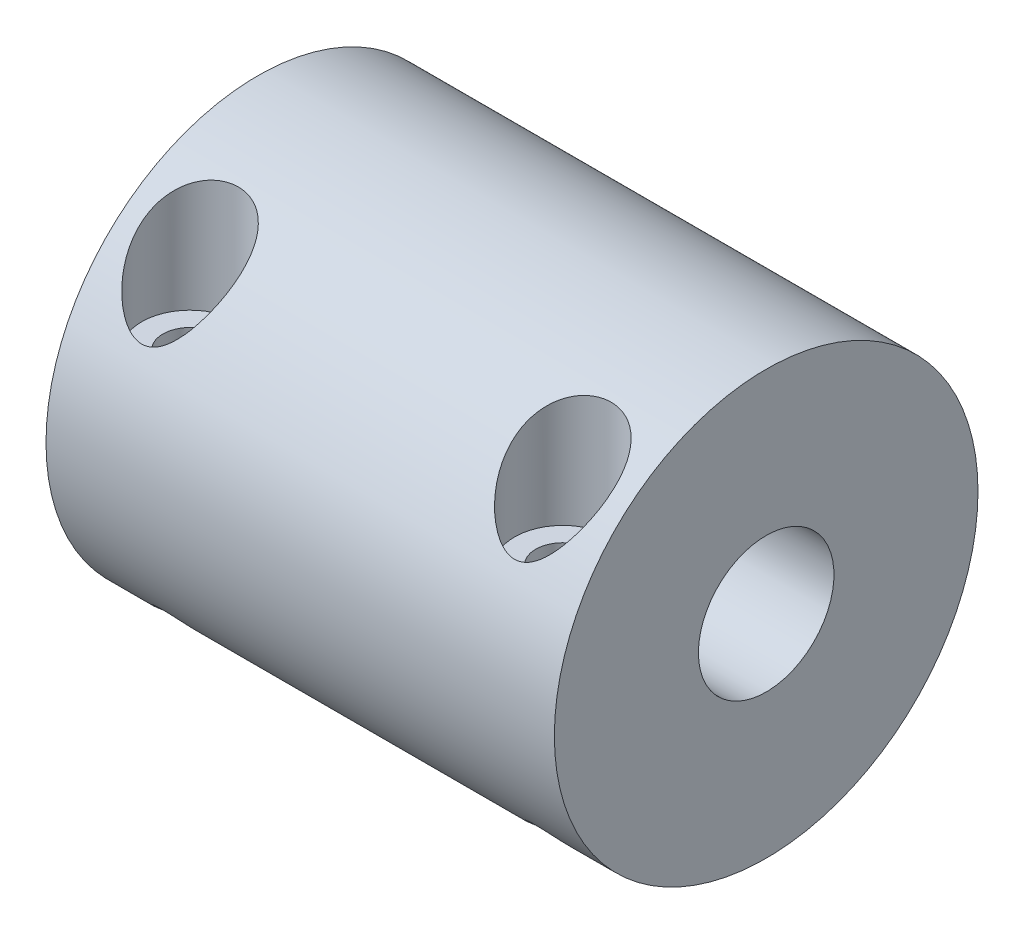
SolidWorks part; units mm, degrees
ref_plane "前视基准面" through (0, 0, 0) normal (0, 0, 1) x (1, 0, 0)
ref_plane "上视基准面" through (0, 0, 0) normal (0, 1, 0) x (1, 0, 0)
ref_plane "右视基准面" through (0, 0, 0) normal (1, 0, 0) x (0, 0, -1)
sketch "草图1" plane through (0, 0, 0) normal (0, 1, 0) x (1, 0, 0)
  line L0 (-118.9427, 0) -> (5828.1908, 0) construction
  line L1 (0, -118.9427) -> (0, 5828.1908) construction
  line L3 (0, 0) -> (30, 0)
  line L4 (0, 0) -> (0, 12.5)
  line L5 (0, 12.5) -> (30, 12.5)
  line L6 (30, 0) -> (30, 12.5)
  line L7 (0, 0) -> (30, 0)
  line L8 (0, 0) -> (0, 3)
  line L9 (0, 3) -> (30, 3)
  line L10 (30, 0) -> (30, 3)
  line L11 (30, 0) -> (15, 0)
  line L12 (30, 0) -> (30, 4)
  line L13 (30, 4) -> (15, 4)
  line L14 (15, 0) -> (15, 4)
  dimension "D1" = 8
  dimension "D2" = 6
  dimension "D3" = 25
  dimension "D4" = 30
  dimension "D5" = 30
  dimension "D6" = 15
revolve "主体" add sketch "草图1" angle 360 about L0
sketch "草图2" plane through (0, 0, 0) normal (0, 1, 0) x (1, 0, 0)
  line L0 (-1000, 0) -> (49000, 0) construction
  line L1 (0, 12.5) -> (0, -12.5) construction
  line L2 (15, -987.5) -> (15, 49012.5) construction
  line L3 (30, 12.5) -> (0, 12.5) construction
  circle A0 centre (4, -8) radius 1.6
  circle A1 centre (26, -8) radius 1.6
  point P5 (0, 0)
  point P10 (15, 12.5)
  dimension "D1" = 3.2
  dimension "D2" = 4
  dimension "D3" = 8
extrude "M3孔" cut sketch "草图2" against normal through all both and the other way through all
sketch3d "3D草图1"
  point P0 (7.9069, 12.4994, 0.1229)
ref_plane "基准面1" through (0, 12.4994, 0) normal (0, 1, 0) x (1, 0, 0)
sketch "草图3" plane through (0, 12.4994, 0) normal (0, 1, 0) x (1, 0, 0)
  circle A0 centre (4, -8) radius 2.85
  circle A1 centre (26, -8) radius 2.85
  circle A2 centre (26, -8) radius 1.6 construction
  dimension "D1" = 5.7
extrude "沉孔" cut sketch "草图3" against normal blind 8
